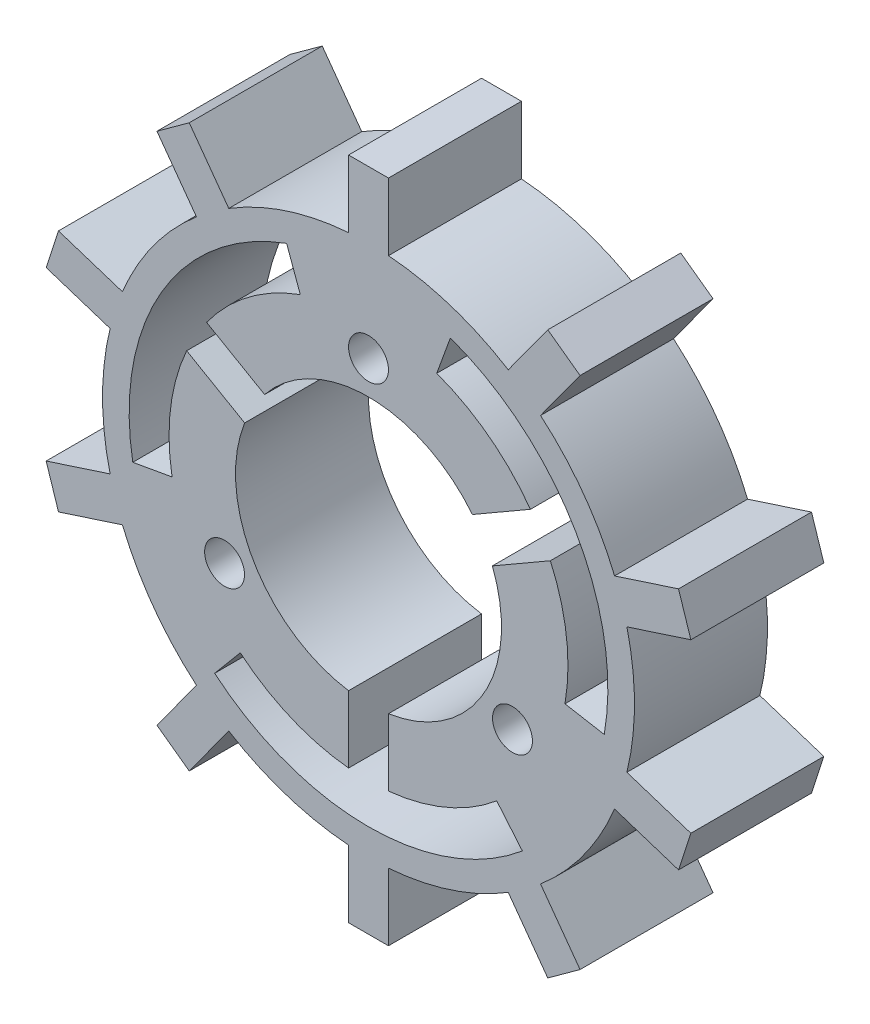
SolidWorks part; units mm, degrees
ref_plane "前视基准面" through (0, 0, 0) normal (0, 0, 1) x (1, 0, 0)
ref_plane "上视基准面" through (0, 0, 0) normal (0, 1, 0) x (1, 0, 0)
ref_plane "右视基准面" through (0, 0, 0) normal (1, 0, 0) x (0, 0, -1)
sketch "草图1" plane through (0, 0, 0) normal (0, 0, 1) x (1, 0, 0)
  line L1 (1.5, 19.9437) -> (1.5, 25)
  line L2 (-1.5, 19.9437) -> (-1.5, 25)
  line L3 (1.5, 25) -> (-1.5, 25)
  line L7 (10.5091, 17.0164) -> (13.4811, 21.1071)
  line L8 (15.9082, 19.3437) -> (13.4811, 21.1071)
  line L9 (12.9361, 15.2531) -> (15.9082, 19.3437)
  line L10 (18.504, 7.5895) -> (23.3129, 9.152)
  line L11 (24.2399, 6.2988) -> (23.3129, 9.152)
  line L12 (19.4311, 4.7363) -> (24.2399, 6.2988)
  line L13 (19.4311, -4.7363) -> (24.2399, -6.2988)
  line L14 (23.3129, -9.152) -> (24.2399, -6.2988)
  line L15 (18.504, -7.5895) -> (23.3129, -9.152)
  line L16 (12.9361, -15.2531) -> (15.9082, -19.3437)
  line L17 (13.4811, -21.1071) -> (15.9082, -19.3437)
  line L18 (10.5091, -17.0164) -> (13.4811, -21.1071)
  line L19 (1.5, -19.9437) -> (1.5, -25)
  line L20 (-1.5, -25) -> (1.5, -25)
  line L21 (-1.5, -19.9437) -> (-1.5, -25)
  line L22 (-10.5091, -17.0164) -> (-13.4811, -21.1071)
  line L23 (-15.9082, -19.3437) -> (-13.4811, -21.1071)
  line L24 (-12.9361, -15.2531) -> (-15.9082, -19.3437)
  line L25 (-18.504, -7.5895) -> (-23.3129, -9.152)
  line L26 (-24.2399, -6.2988) -> (-23.3129, -9.152)
  line L27 (-19.4311, -4.7363) -> (-24.2399, -6.2988)
  line L28 (-19.4311, 4.7363) -> (-24.2399, 6.2988)
  line L29 (-23.3129, 9.152) -> (-24.2399, 6.2988)
  line L30 (-18.504, 7.5895) -> (-23.3129, 9.152)
  line L31 (-12.9361, 15.2531) -> (-15.9082, 19.3437)
  line L32 (-13.4811, 21.1071) -> (-15.9082, 19.3437)
  line L33 (-10.5091, 17.0164) -> (-13.4811, 21.1071)
  arc A0 (-18.504, -7.5895) -> (-12.9361, -15.2531) centre (0, 0) ccw
  circle A1 centre (0, 12.5) radius 1.5
  circle A2 centre (10.8253, -6.25) radius 1.5
  circle A3 centre (-10.8253, -6.25) radius 1.5
  arc A4 (-19.4311, 4.7363) -> (-19.4311, -4.7363) centre (0, 0) ccw
  arc A5 (-12.9361, 15.2531) -> (-18.504, 7.5895) centre (0, 0) ccw
  arc A6 (-1.5, 19.9437) -> (-10.5091, 17.0164) centre (0, 0) ccw
  arc A7 (10.5091, 17.0164) -> (1.5, 19.9437) centre (0, 0) ccw
  arc A8 (18.504, 7.5895) -> (12.9361, 15.2531) centre (0, 0) ccw
  arc A9 (19.4311, -4.7363) -> (19.4311, 4.7363) centre (0, 0) ccw
  arc A10 (12.9361, -15.2531) -> (18.504, -7.5895) centre (0, 0) ccw
  arc A11 (1.5, -19.9437) -> (10.5091, -17.0164) centre (0, 0) ccw
  arc A12 (-10.5091, -17.0164) -> (-1.5, -19.9437) centre (0, 0) ccw
  point P50 (0, 0)
  point P52 (0, 0)
  dimension "D1" = 40
  dimension "D4" = 3
  dimension "D2" = 10
  dimension "D3" = 12.5
  dimension "D5" = 3
extrude "凸台-拉伸1" add sketch "草图1" along normal blind 10
sketch "草图2" plane through (0, 0, 0) normal (0, 0, 1) x (1, 0, 0)
  line L0 (-9.3123, 3.6444) -> (-13.6753, 6.1634)
  line L1 (-7.8123, 6.2425) -> (-12.1753, 8.7614)
  line L2 (-5.1303, 14.0954) -> (-6.1564, 16.9145)
  line L3 (-14.7721, -2.6047) -> (-17.7265, -3.1257)
  line L4 (-9.6418, -11.4907) -> (-11.5702, -13.7888)
  line L5 (9.6418, -11.4907) -> (11.5702, -13.7888)
  line L6 (-1.5, -9.8869) -> (-1.5, -14.9248)
  line L7 (7.8123, 6.2425) -> (12.1753, 8.7614)
  line L8 (1.5, -9.8869) -> (1.5, -14.9248)
  line L9 (9.3123, 3.6444) -> (13.6753, 6.1634)
  line L10 (14.7721, -2.6047) -> (17.7265, -3.1257)
  line L11 (5.1303, 14.0954) -> (6.1564, 16.9145)
  arc A0 (1.5, -9.8869) -> (9.3123, 3.6444) centre (0, 0) ccw
  arc A1 (-11.5702, -13.7888) -> (11.5702, -13.7888) centre (0, 0) ccw
  arc A2 (1.5, -14.9248) -> (9.6418, -11.4907) centre (0, 0) ccw
  arc A3 (-9.6418, -11.4907) -> (-1.5, -14.9248) centre (0, 0) ccw
  arc A4 (-5.1303, 14.0954) -> (-12.1753, 8.7614) centre (0, 0) ccw
  arc A5 (-13.6753, 6.1634) -> (-14.7721, -2.6047) centre (0, 0) ccw
  arc A6 (-6.1564, 16.9145) -> (-17.7265, -3.1257) centre (0, 0) ccw
  arc A7 (14.7721, -2.6047) -> (13.6753, 6.1634) centre (0, 0) ccw
  arc A8 (12.1753, 8.7614) -> (5.1303, 14.0954) centre (0, 0) ccw
  arc A9 (17.7265, -3.1257) -> (6.1564, 16.9145) centre (0, 0) ccw
  arc A10 (7.8123, 6.2425) -> (-7.8123, 6.2425) centre (0, 0) ccw
  arc A11 (-9.3123, 3.6444) -> (-1.5, -9.8869) centre (0, 0) ccw
  point P29 (0, 0)
  dimension "D1" = 20
  dimension "D4" = 36
  dimension "D5" = 30
  dimension "D2" = 3
extrude "切除-拉伸2" cut sketch "草图2" along normal blind 10
